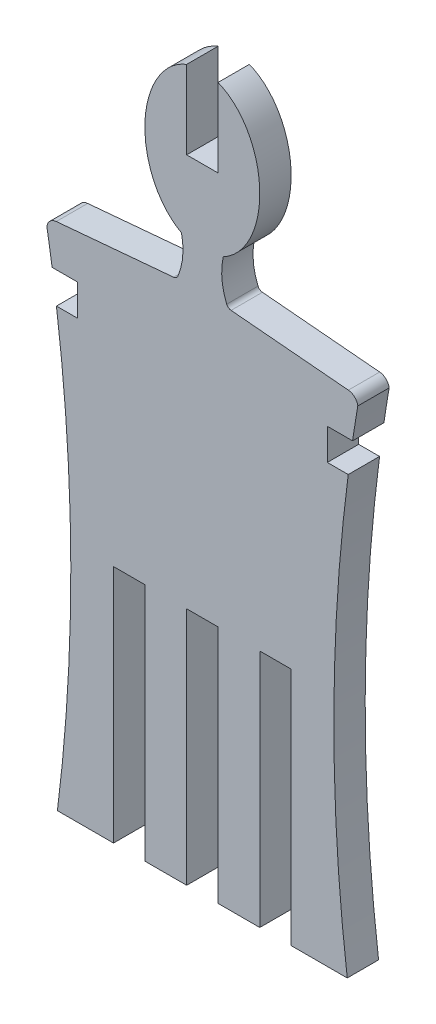
SolidWorks part; units mm, degrees
ref_plane "Front Plane" through (0, 0, 0) normal (0, 0, 1) x (1, 0, 0)
ref_plane "Top Plane" through (0, 0, 0) normal (0, 1, 0) x (1, 0, 0)
ref_plane "Right Plane" through (0, 0, 0) normal (1, 0, 0) x (0, 0, -1)
sketch "Sketch3" plane through (0, 0, 0) normal (0, 0, 1) x (1, 0, 0)
  line L0 (0, 48.0962) -> (0, -91.1755) construction
  line L4 (1.5, -40.7983) -> (1.5, -17.8779)
  line L5 (-56.8903, 0) -> (51.432, 0) construction
  line L6 (1.5, -17.8779) -> (-1.5, -17.8779)
  line L7 (2.75, 8.9823) -> (13.977, 7.9844)
  line L8 (5.5, -40.7983) -> (5.5, -17.8779)
  line L9 (5.5, -17.8779) -> (8.5, -17.8779)
  line L10 (8.5, -17.8779) -> (8.5, -40.7983)
  line L12 (11.9635, 3.9831) -> (14.3816, 3.9831)
  line L13 (13.9635, 0.9831) -> (11.9635, 0.9831)
  line L14 (11.9635, 0.9831) -> (11.9635, 3.9831)
  line L15 (-1.5, -40.7983) -> (-1.5, -17.8779)
  line L16 (-5.5, -40.7983) -> (-5.5, -17.8779)
  line L17 (-5.5, -17.8779) -> (-8.5, -17.8779)
  line L18 (-8.5, -17.8779) -> (-8.5, -40.7983)
  line L19 (-13.9635, 0.9831) -> (-11.9635, 0.9831)
  line L20 (-11.9635, 0.9831) -> (-11.9635, 3.9831)
  line L21 (-11.9635, 3.9831) -> (-14.3816, 3.9831)
  line L22 (-2.75, 8.9823) -> (-13.977, 7.9844)
  line L23 (1.5, 27.2494) -> (1.5, 19.7494)
  line L24 (1.5, 19.7494) -> (-1.5, 19.7494)
  line L25 (-1.5, 27.2494) -> (-1.5, 19.7494)
  line L26 (-8.5, -40.7983) -> (-13.8696, -40.7983)
  line L27 (-1.5, -40.7983) -> (-5.5, -40.7983)
  line L28 (13.8696, -40.7983) -> (8.5, -40.7983)
  line L29 (5.5, -40.7983) -> (1.5, -40.7983)
  arc A0 (13.977, 7.9844) -> (14.8794, 7.1221) centre (13.8884, 6.9883) cw
  arc A1 (14.8794, 7.1221) -> (14.3816, 3.9831) centre (177.4699, -20.2751) ccw
  arc A3 (-2.75, 8.9823) -> (-2.3328, 9.2878) centre (-2.7943, 9.4804) ccw
  arc A4 (-2, 13.0472) -> (-2.3328, 9.2878) centre (-8.0938, 11.6923) cw
  arc A5 (13.9635, 0.9831) -> (13.8696, -40.7983) centre (177.4699, -20.2751) ccw
  arc A9 (-13.9635, 0.9831) -> (-13.8696, -40.7983) centre (-177.4699, -20.2751) cw
  arc A10 (-14.8794, 7.1221) -> (-14.3816, 3.9831) centre (-177.4699, -20.2751) cw
  arc A11 (-13.977, 7.9844) -> (-14.8794, 7.1221) centre (-13.8884, 6.9883) ccw
  arc A12 (2, 13.0472) -> (2.3328, 9.2878) centre (8.0938, 11.6923) ccw
  arc A13 (2.75, 8.9823) -> (2.3328, 9.2878) centre (2.7943, 9.4804) cw
  ellipse E0 centre (0, 20.0337) end of major axis (0, 12.5337) minor radius 5.5 (2, 13.0472) -> (1.5, 27.2494) ccw
  ellipse E1 centre (0, 20.0337) end of major axis (0, 12.5337) minor radius 5.5 (-1.5, 27.2494) -> (-2, 13.0472) ccw
  point P16 (14.1439, -42.8779)
  point P42 (0, 19.7494)
  point P47 (0, -17.8779)
  dimension "D1" = 1
  dimension "D3" = 4
  dimension "D2" = 0.5
  dimension "D4" = 50
  dimension "D6" = 15
  dimension "D7" = 5.5
  dimension "D8" = 1.5
  dimension "D9" = 5.08
  dimension "D10" = 11
  dimension "D11" = 3
  dimension "D12" = 1.5
  dimension "D14" = 7.5
  dimension "D17" = 3
  dimension "D18" = 2
  dimension "D19" = 1.8603
extrude "Boss-Extrude3" add sketch "Sketch3" along normal blind 3
